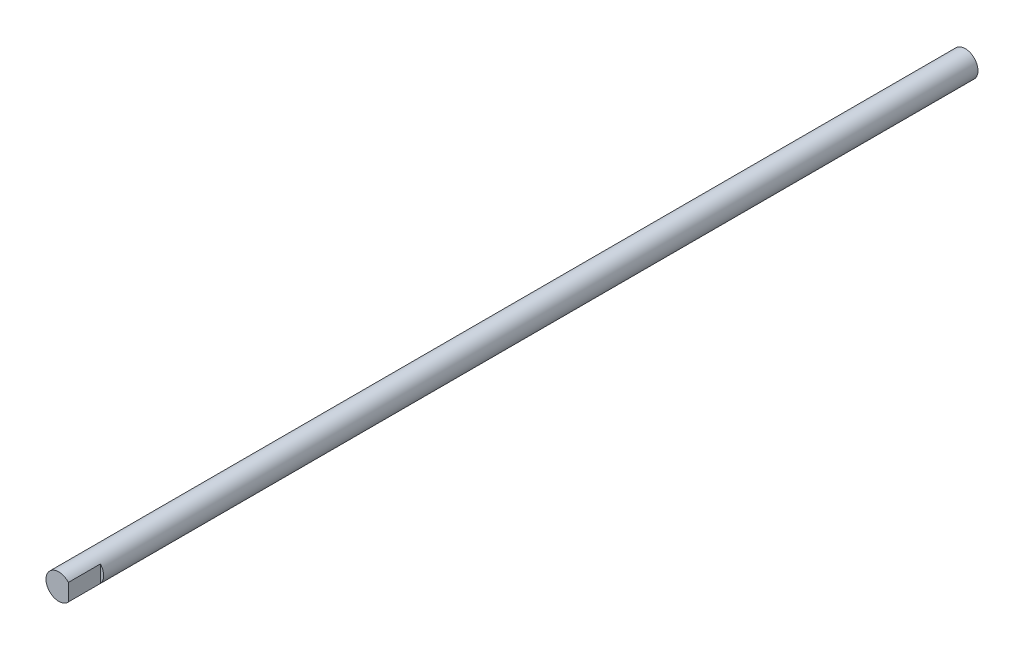
SolidWorks part; units mm, degrees
material "Acero al carbono no aleado"
ref_plane "Front Plane" through (0, 0, 0) normal (0, 0, 1) x (1, 0, 0)
ref_plane "Top Plane" through (0, 0, 0) normal (0, 1, 0) x (1, 0, 0)
ref_plane "Right Plane" through (0, 0, 0) normal (1, 0, 0) x (0, 0, -1)
sketch "Sketch1" plane through (0, 0, 0) normal (0, 0, 1) x (1, 0, 0)
  circle A0 centre (0, 0) radius 4
  dimension "D1" = 8
extrude "Boss-Extrude1" add sketch "Sketch1" against normal blind 283
sketch "Sketch2" plane through (0, 0, 0) normal (0, 0, 1) x (1, 0, 0)
  circle A0 centre (0, 0) radius 4
  dimension "D1" = 8
curve "Helix/Spiral1" pitch 2 height 300 turns 150
sketch "Croquis1" plane through (0, 0, 0) normal (0, 0, 1) x (1, 0, 0)
  line L1 (3, 5.2968) -> (14.4733, 5.2968)
  line L2 (3, 5.2968) -> (3, -6.8277)
  line L3 (3, -6.8277) -> (14.4733, -6.8277)
  line L4 (14.4733, 5.2968) -> (14.4733, -6.8277)
  dimension "D1" = 3
extrude "Cortar-Extruir1" cut sketch "Croquis1" against normal blind 10
